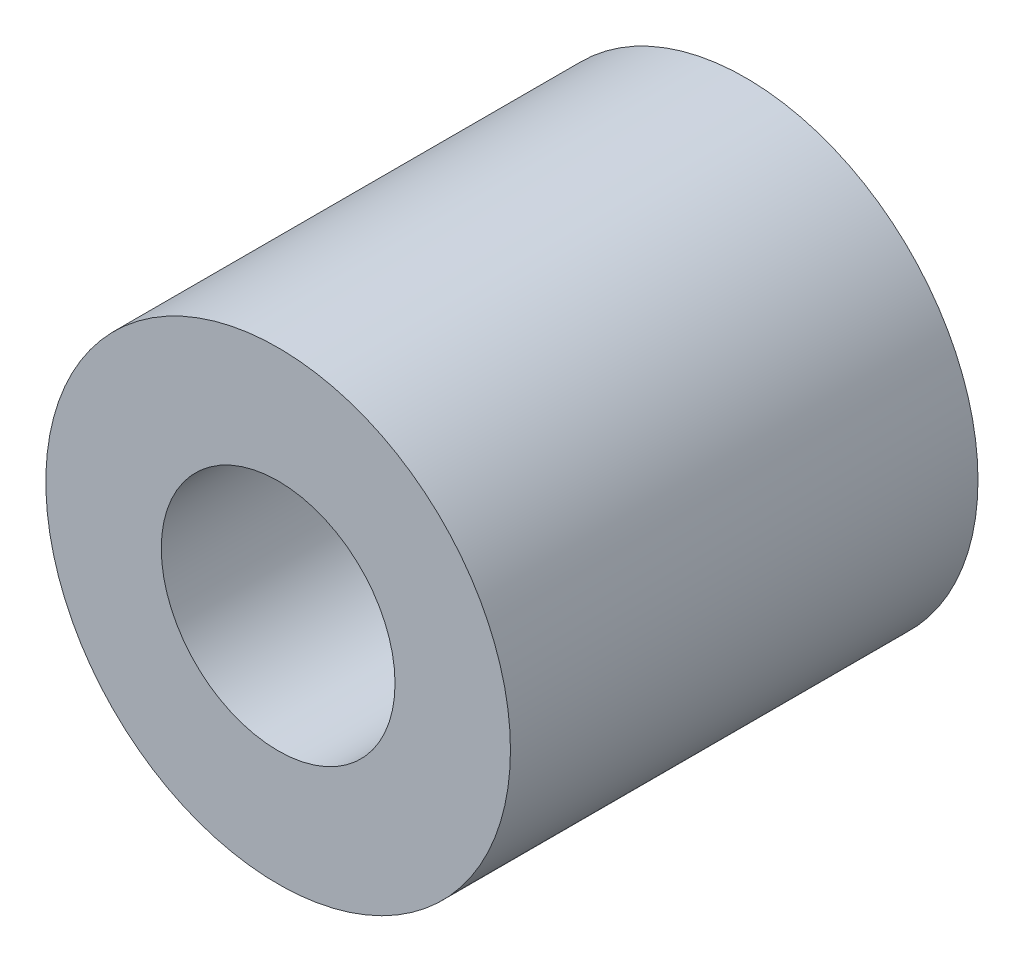
SolidWorks part; units mm, degrees
material "Plain Carbon Steel"
ref_plane "Front Plane" through (0, 0, 0) normal (0, 0, 1) x (1, 0, 0)
ref_plane "Top Plane" through (0, 0, 0) normal (0, 1, 0) x (1, 0, 0)
ref_plane "Right Plane" through (0, 0, 0) normal (1, 0, 0) x (0, 0, -1)
sketch "Sketch1" plane through (0, 0, 0) normal (0, 0, 1) x (1, 0, 0)
  circle A0 centre (0, 0) radius 4
  circle A1 centre (0, 0) radius 7.95
  dimension "D1" = 8
  dimension "D2" = 15.9
extrude "Boss-Extrude1" add sketch "Sketch1" along normal blind 16
